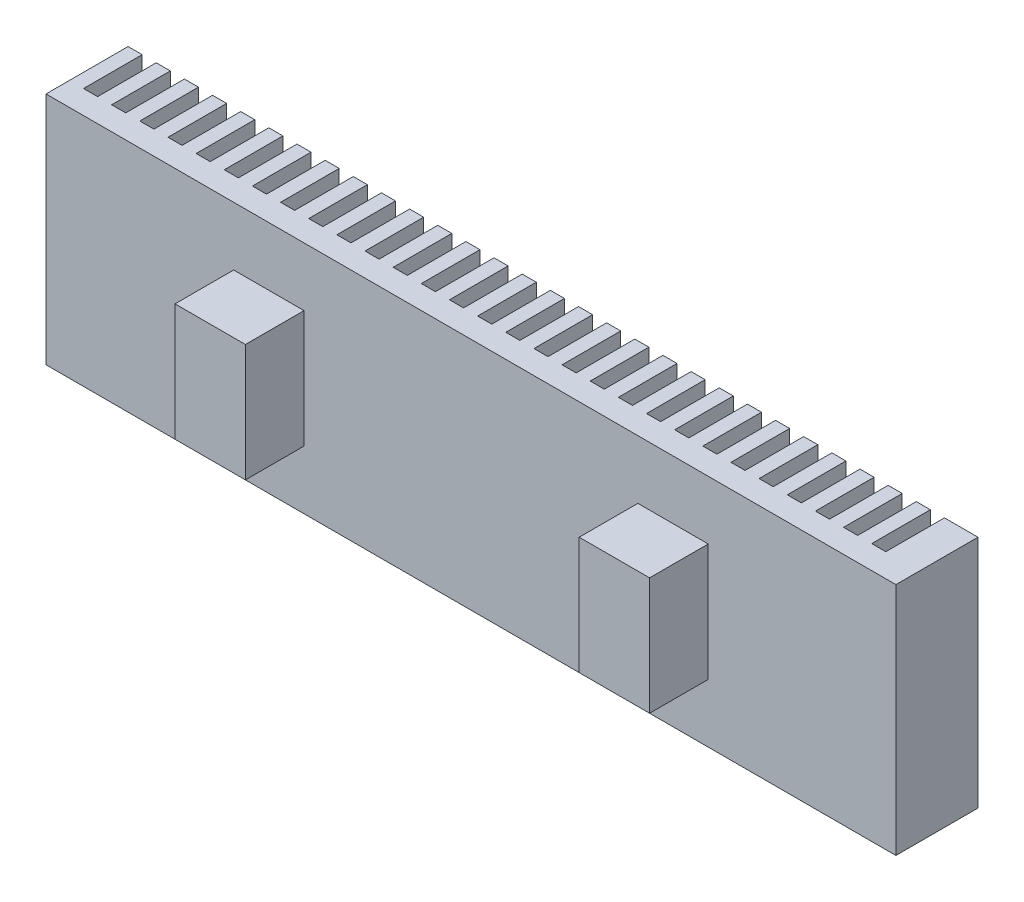
SolidWorks part; units mm, degrees
ref_plane "Front Plane" through (0, 0, 0) normal (0, 0, 1) x (1, 0, 0)
ref_plane "Top Plane" through (0, 0, 0) normal (0, 1, 0) x (1, 0, 0)
ref_plane "Right Plane" through (0, 0, 0) normal (1, 0, 0) x (0, 0, -1)
sketch "Sketch1" plane through (0, 0, 0) normal (0, 1, 0) x (1, 0, 0)
  line L1 (0, 0) -> (-36.23, 0)
  line L2 (0, 0) -> (0, 3.5)
  line L3 (0, 3.5) -> (-36.23, 3.5)
  line L4 (-36.23, 0) -> (-36.23, 3.5)
  dimension "D1" = 36.23
  dimension "D2" = 3.5
extrude "Boss-Extrude1" add sketch "Sketch1" along normal blind 10
sketch "Sketch3" plane through (0, 0, 0) normal (0, 0, 1) x (1, 0, 0)
  line L0 (-36.23, 10) -> (-36.23, 0) construction
  line L1 (-28.23, 7.5) -> (-25.23, 7.5)
  line L2 (-28.23, 7.5) -> (-28.23, 2.5)
  line L3 (-28.23, 2.5) -> (-25.23, 2.5)
  line L4 (-25.23, 7.5) -> (-25.23, 2.5)
  line L5 (-36.23, 5) -> (0, 5) construction
  line L6 (0, 10) -> (0, 0) construction
  line L8 (-11, 7.5) -> (-8, 7.5)
  line L9 (-11, 7.5) -> (-11, 2.5)
  line L10 (-11, 2.5) -> (-8, 2.5)
  line L11 (-8, 7.5) -> (-8, 2.5)
  dimension "D1" = 3
  dimension "D2" = 5
  dimension "D3" = 8
  dimension "D4" = 5
  dimension "D5" = 3
  dimension "D6" = 8
extrude "Boss-Extrude2" add sketch "Sketch3" along normal blind 2.5
sketch "Sketch4" plane through (0, 10, 0) normal (0, 1, 0) x (1, 0, 0)
  line L0 (0, 3.5) -> (-36.23, 3.5) construction
  line L1 (-35.63, 3.5) -> (-35.03, 3.5)
  line L2 (-35.63, 3.5) -> (-35.63, 1)
  line L3 (-35.63, 1) -> (-35.03, 1)
  line L4 (-35.03, 3.5) -> (-35.03, 1)
  line L5 (-36.23, 0) -> (-36.23, 3.5) construction
  dimension "D1" = 0.6
  dimension "D2" = 2.5
  dimension "D3" = 0.6
extrude "Cut-Extrude1" cut sketch "Sketch4" against normal through all
pattern_linear "LPattern1" count 29 spacing 1.2 along (1, 0, 0) of "Cut-Extrude1"
